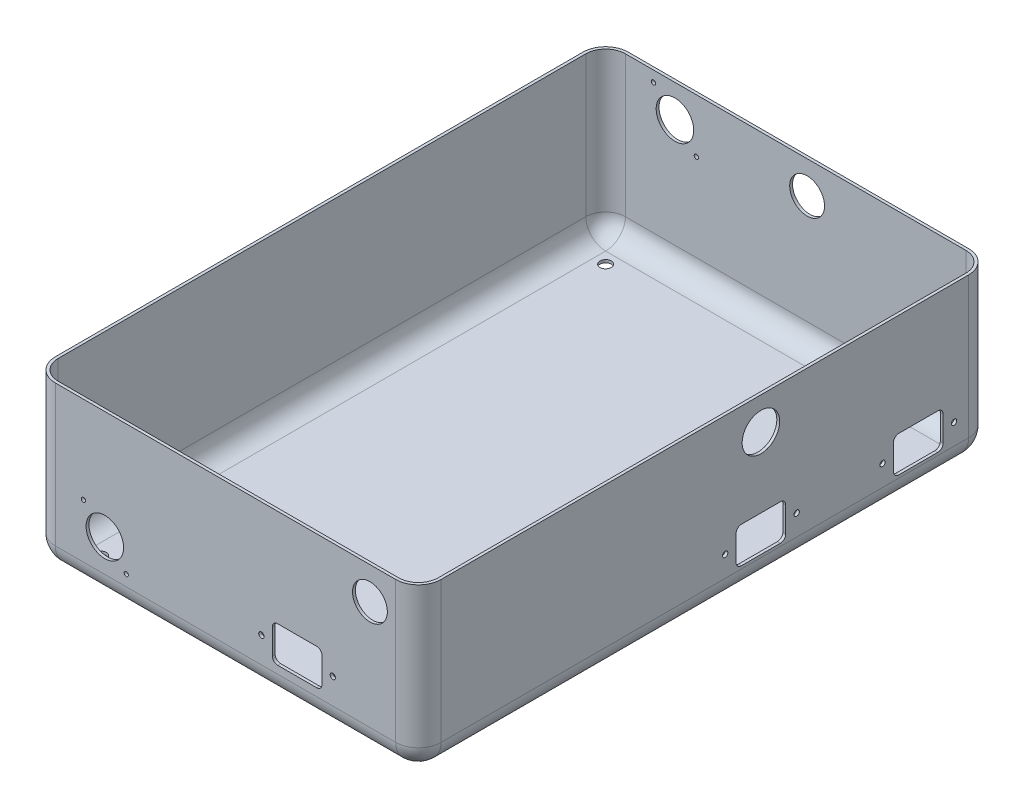
SolidWorks part; units mm, degrees
ref_plane "Front" through (0, 0, 0) normal (0, 0, 1) x (1, 0, 0)
ref_plane "Top" through (0, 0, 0) normal (0, 1, 0) x (1, 0, 0)
ref_plane "Right" through (0, 0, 0) normal (1, 0, 0) x (0, 0, -1)
sketch "Sketch1" plane through (0, 0, 0) normal (0, 1, 0) x (1, 0, 0)
  line L1 (0, 0) -> (215.9, 0)
  line L2 (0, 0) -> (0, 320.675)
  line L3 (0, 320.675) -> (215.9, 320.675)
  line L4 (215.9, 0) -> (215.9, 320.675)
  dimension "D1" = 215.9
  dimension "D2" = 320.675
extrude "Boss-Extrude1" add sketch "Sketch1" along normal blind 91.6889 contours L1 L4 L3 L2
fillet "Fillet1" radius 12.7 8 edges at (0, 45.8445, -320.675) (215.9, 45.8445, -320.675) (215.9, 45.8445, 0) (0, 45.8445, 0) (107.95, 0, -320.675) (0, 0, -160.3375) (107.95, 0, 0) (215.9, 0, -160.3375)
shell "Shell1" thickness 1.6002
sketch "Sketch2" plane through (215.9, 0, 0) normal (1, 0, 0) x (0, 0, -1)
  line L0 (168.1645, 20.8147) -> (175.0003, 13.9789) construction
  line L1 (177.1216, 13.1002) -> (206.2784, 13.1002) construction
  line L2 (208.3997, 13.9789) -> (215.2355, 20.8147) construction
  line L3 (215.2355, 27.8857) -> (208.3997, 34.7215) construction
  line L4 (206.2784, 35.6002) -> (177.1216, 35.6002) construction
  line L5 (175.0003, 34.7215) -> (168.1645, 27.8857) construction
  line L7 (307.975, 12.7) -> (307.975, 91.6889) construction
  line L9 (12.7, 91.6889) -> (12.7, 12.7) construction
  line L10 (168.1645, 20.8147) -> (175.0003, 13.9789)
  line L11 (177.1216, 13.1002) -> (206.2784, 13.1002)
  line L12 (208.3997, 13.9789) -> (215.2355, 20.8147)
  line L13 (215.2355, 27.8857) -> (208.3997, 34.7215)
  line L14 (206.2784, 35.6002) -> (177.1216, 35.6002)
  line L15 (175.0003, 34.7215) -> (168.1645, 27.8857)
  line L16 (12.7, 12.7) -> (307.975, 12.7)
  line L17 (307.975, 12.7) -> (307.975, 91.6889)
  line L18 (307.975, 91.6889) -> (12.7, 91.6889)
  line L19 (12.7, 91.6889) -> (12.7, 12.7)
  line L20 (205.6, 31.4002) -> (205.6, 17.3002) construction
  line L21 (202.6, 14.3002) -> (180.8, 14.3002) construction
  line L22 (177.8, 17.3002) -> (177.8, 31.4002) construction
  line L23 (180.8, 34.4002) -> (202.6, 34.4002) construction
  line L24 (293.7, 31.4002) -> (293.7, 17.3002) construction
  line L25 (290.7, 14.3002) -> (268.9, 14.3002) construction
  line L26 (256.2645, 20.8147) -> (263.1003, 13.9789)
  line L27 (265.2216, 13.1002) -> (294.3784, 13.1002)
  line L28 (296.4997, 13.9789) -> (303.3355, 20.8147)
  line L29 (303.3355, 27.8857) -> (296.4997, 34.7215)
  line L30 (294.3784, 35.6002) -> (265.2216, 35.6002)
  line L31 (263.1003, 34.7215) -> (256.2645, 27.8857)
  line L32 (256.2645, 20.8147) -> (263.1003, 13.9789)
  line L33 (265.2216, 13.1002) -> (294.3784, 13.1002)
  line L34 (296.4997, 13.9789) -> (303.3355, 20.8147)
  line L35 (303.3355, 27.8857) -> (296.4997, 34.7215)
  line L36 (294.3784, 35.6002) -> (265.2216, 35.6002)
  line L37 (263.1003, 34.7215) -> (256.2645, 27.8857)
  line L38 (265.9, 17.3002) -> (265.9, 31.4002) construction
  line L39 (268.9, 34.4002) -> (290.7, 34.4002) construction
  line L40 (205.6, 31.4002) -> (205.6, 17.3002)
  line L41 (202.6, 14.3002) -> (180.8, 14.3002)
  line L42 (177.8, 17.3002) -> (177.8, 31.4002)
  line L43 (180.8, 34.4002) -> (202.6, 34.4002)
  line L44 (293.7, 31.4002) -> (293.7, 17.3002)
  line L45 (290.7, 14.3002) -> (268.9, 14.3002)
  line L46 (265.9, 17.3002) -> (265.9, 31.4002)
  line L47 (268.9, 34.4002) -> (290.7, 34.4002)
  line L48 (12.7, 12.7) -> (307.975, 12.7) construction
  line L49 (12.7, 91.6889) -> (307.975, 91.6889) construction
  arc A0 (168.1645, 27.8857) -> (168.1645, 20.8147) centre (171.7, 24.3502) ccw construction
  arc A1 (175.0003, 13.9789) -> (177.1216, 13.1002) centre (177.1216, 16.1002) ccw construction
  arc A2 (206.2784, 13.1002) -> (208.3997, 13.9789) centre (206.2784, 16.1002) ccw construction
  arc A3 (215.2355, 20.8147) -> (215.2355, 27.8857) centre (211.7, 24.3502) ccw construction
  arc A4 (208.3997, 34.7215) -> (206.2784, 35.6002) centre (206.2784, 32.6002) ccw construction
  arc A5 (177.1216, 35.6002) -> (175.0003, 34.7215) centre (177.1216, 32.6002) ccw construction
  arc A6 (168.1645, 27.8857) -> (168.1645, 20.8147) centre (171.7, 24.3502) ccw
  arc A7 (175.0003, 13.9789) -> (177.1216, 13.1002) centre (177.1216, 16.1002) ccw
  arc A8 (206.2784, 13.1002) -> (208.3997, 13.9789) centre (206.2784, 16.1002) ccw
  arc A9 (215.2355, 20.8147) -> (215.2355, 27.8857) centre (211.7, 24.3502) ccw
  arc A10 (208.3997, 34.7215) -> (206.2784, 35.6002) centre (206.2784, 32.6002) ccw
  arc A11 (177.1216, 35.6002) -> (175.0003, 34.7215) centre (177.1216, 32.6002) ccw
  circle A12 centre (171.7, 24.3502) radius 1.5 construction
  circle A13 centre (211.7, 24.3502) radius 1.5 construction
  circle A14 centre (171.7, 24.3502) radius 1.5
  circle A15 centre (211.7, 24.3502) radius 1.5
  arc A16 (200.8, 78.8704) -> (200.1022, 67.3349) centre (191.7, 73.6321) ccw construction
  arc A17 (200.8, 78.8704) -> (202.2, 73.6321) centre (191.7, 73.6321) ccw
  arc A19 (200.8, 78.8704) -> (202.2, 73.6321) centre (191.7, 73.6321) cw
  circle A20 centre (299.8, 24.3502) radius 1.5 construction
  circle A21 centre (259.8, 24.3502) radius 1.5 construction
  circle A22 centre (299.8, 24.3502) radius 1.5
  circle A23 centre (259.8, 24.3502) radius 1.5
  arc A24 (205.6, 31.4002) -> (202.6, 34.4002) centre (202.6, 31.4002) ccw construction
  arc A25 (202.6, 14.3002) -> (205.6, 17.3002) centre (202.6, 17.3002) ccw construction
  arc A26 (177.8, 17.3002) -> (180.8, 14.3002) centre (180.8, 17.3002) ccw construction
  arc A27 (180.8, 34.4002) -> (177.8, 31.4002) centre (180.8, 31.4002) ccw construction
  arc A28 (293.7, 31.4002) -> (290.7, 34.4002) centre (290.7, 31.4002) ccw construction
  arc A29 (290.7, 14.3002) -> (293.7, 17.3002) centre (290.7, 17.3002) ccw construction
  arc A30 (256.2645, 27.8857) -> (256.2645, 20.8147) centre (259.8, 24.3502) ccw
  arc A31 (263.1003, 13.9789) -> (265.2216, 13.1002) centre (265.2216, 16.1002) ccw
  arc A32 (294.3784, 13.1002) -> (296.4997, 13.9789) centre (294.3784, 16.1002) ccw
  arc A33 (303.3355, 20.8147) -> (303.3355, 27.8857) centre (299.8, 24.3502) ccw
  arc A34 (296.4997, 34.7215) -> (294.3784, 35.6002) centre (294.3784, 32.6002) ccw
  arc A35 (265.2216, 35.6002) -> (263.1003, 34.7215) centre (265.2216, 32.6002) ccw
  arc A36 (256.2645, 27.8857) -> (256.2645, 20.8147) centre (259.8, 24.3502) ccw
  arc A37 (263.1003, 13.9789) -> (265.2216, 13.1002) centre (265.2216, 16.1002) ccw
  arc A38 (294.3784, 13.1002) -> (296.4997, 13.9789) centre (294.3784, 16.1002) ccw
  arc A39 (303.3355, 20.8147) -> (303.3355, 27.8857) centre (299.8, 24.3502) ccw
  arc A40 (296.4997, 34.7215) -> (294.3784, 35.6002) centre (294.3784, 32.6002) ccw
  arc A41 (265.2216, 35.6002) -> (263.1003, 34.7215) centre (265.2216, 32.6002) ccw
  arc A42 (265.9, 17.3002) -> (268.9, 14.3002) centre (268.9, 17.3002) ccw construction
  arc A43 (268.9, 34.4002) -> (265.9, 31.4002) centre (268.9, 31.4002) ccw construction
  arc A44 (205.6, 31.4002) -> (202.6, 34.4002) centre (202.6, 31.4002) ccw
  arc A45 (202.6, 14.3002) -> (205.6, 17.3002) centre (202.6, 17.3002) ccw
  arc A46 (177.8, 17.3002) -> (180.8, 14.3002) centre (180.8, 17.3002) ccw
  arc A47 (180.8, 34.4002) -> (177.8, 31.4002) centre (180.8, 31.4002) ccw
  arc A48 (293.7, 31.4002) -> (290.7, 34.4002) centre (290.7, 31.4002) ccw
  arc A49 (290.7, 14.3002) -> (293.7, 17.3002) centre (290.7, 17.3002) ccw
  arc A50 (265.9, 17.3002) -> (268.9, 14.3002) centre (268.9, 17.3002) ccw
  arc A51 (268.9, 34.4002) -> (265.9, 31.4002) centre (268.9, 31.4002) ccw
  dimension "D1" = 0
extrude "Cut-Extrude1" cut sketch "Sketch2" against normal up to next contours A19 A17 | A14 | A15 | A23 | A22 | L47 A51 L46 A50 L45 A49 L44 A48 | L43 A47 L42 A46 L41 A45 L40 A44
sketch "Sketch5" plane through (317.5, 0, 0) normal (0, 0, 1) x (1, 0, 0)
  line L0 (-180.375, 37.175) -> (-158.575, 37.175) construction
  line L1 (-183.375, 20.075) -> (-183.375, 34.175) construction
  line L2 (-158.575, 17.075) -> (-180.375, 17.075) construction
  line L3 (-155.575, 34.175) -> (-155.575, 20.075) construction
  line L4 (-180.375, 37.175) -> (-158.575, 37.175)
  line L5 (-183.375, 20.075) -> (-183.375, 34.175)
  line L6 (-158.575, 17.075) -> (-180.375, 17.075)
  line L7 (-155.575, 34.175) -> (-155.575, 20.075)
  arc A2 (-123.85, 65.1883) -> (-133.6, 82.0758) centre (-128.725, 73.6321) ccw construction
  arc A3 (-133.6, 82.0758) -> (-123.85, 65.1883) centre (-128.725, 73.6321) ccw construction
  arc A6 (-123.85, 65.1883) -> (-133.6, 82.0758) centre (-128.725, 73.6321) ccw
  arc A7 (-133.6, 82.0758) -> (-123.85, 65.1883) centre (-128.725, 73.6321) ccw
  circle A8 centre (-189.475, 27.125) radius 1.5 construction
  circle A9 centre (-149.475, 27.125) radius 1.5 construction
  arc A10 (-155.575, 34.175) -> (-158.575, 37.175) centre (-158.575, 34.175) ccw construction
  arc A11 (-180.375, 37.175) -> (-183.375, 34.175) centre (-180.375, 34.175) ccw construction
  arc A12 (-183.375, 20.075) -> (-180.375, 17.075) centre (-180.375, 20.075) ccw construction
  arc A13 (-158.575, 17.075) -> (-155.575, 20.075) centre (-158.575, 20.075) ccw construction
  circle A14 centre (-189.475, 27.125) radius 1.5
  circle A15 centre (-149.475, 27.125) radius 1.5
  arc A16 (-155.575, 34.175) -> (-158.575, 37.175) centre (-158.575, 34.175) ccw
  arc A17 (-180.375, 37.175) -> (-183.375, 34.175) centre (-180.375, 34.175) ccw
  arc A18 (-183.375, 20.075) -> (-180.375, 17.075) centre (-180.375, 20.075) ccw
  arc A19 (-158.575, 17.075) -> (-155.575, 20.075) centre (-158.575, 20.075) ccw
  circle A20 centre (-289.1, 42.875) radius 1.2 construction
  circle A21 centre (-265.1, 18.875) radius 1.2 construction
  circle A22 centre (-277.1, 30.875) radius 10.5 construction
  circle A23 centre (-289.1, 42.875) radius 1.2
  circle A24 centre (-265.1, 18.875) radius 1.2
  circle A25 centre (-277.1, 30.875) radius 10.5
extrude "Cut-Extrude2" cut sketch "Sketch5" against normal up to next
sketch "Sketch6" plane through (0, 0, -320.675) normal (0, 0, -1) x (-1, 0, 0)
  arc A0 (-109.5052, 65.1883) -> (-119.2552, 82.0758) centre (-114.3802, 73.6321) ccw construction
  arc A1 (-119.2552, 82.0758) -> (-109.5052, 65.1883) centre (-114.3802, 73.6321) ccw construction
  arc A2 (-109.5052, 65.1883) -> (-119.2552, 82.0758) centre (-114.3802, 73.6321) ccw
  arc A3 (-119.2552, 82.0758) -> (-109.5052, 65.1883) centre (-114.3802, 73.6321) ccw
  circle A4 centre (-28.4, 85.6321) radius 1.2 construction
  circle A5 centre (-52.4, 61.6321) radius 1.2 construction
  circle A6 centre (-40.4, 73.6321) radius 10.5 construction
  circle A7 centre (-28.4, 85.6321) radius 1.2
  circle A8 centre (-52.4, 61.6321) radius 1.2
  circle A9 centre (-40.4, 73.6321) radius 10.5
extrude "Cut-Extrude3" cut sketch "Sketch6" against normal up to next
sketch "Sketch7" plane through (0, 0, 0) normal (0, -1, 0) x (1, 0, 0)
  line L0 (203.2, -12.7) -> (12.7, -12.7) construction
  line L1 (203.2, -307.975) -> (203.2, -12.7) construction
  line L2 (12.7, -307.975) -> (203.2, -307.975) construction
  line L3 (12.7, -12.7) -> (12.7, -307.975) construction
  line L4 (203.2, -12.7) -> (12.7, -12.7) construction
  line L5 (203.2, -307.975) -> (203.2, -12.7) construction
  line L6 (12.7, -307.975) -> (203.2, -307.975) construction
  line L7 (12.7, -12.7) -> (12.7, -307.975) construction
  line L8 (19.05, -301.625) -> (196.85, -301.625) construction
  line L9 (196.85, -301.625) -> (196.85, -19.05) construction
  line L10 (196.85, -19.05) -> (19.05, -19.05) construction
  line L11 (19.05, -19.05) -> (19.05, -301.625) construction
  line L12 (190.5, -298.4455) -> (190.5, -283.4471) construction
  line L15 (192.0536, -301.625) -> (188.9464, -301.625) construction
  line L16 (188.9464, 9.6951) -> (188.9464, -330.3701) construction
  line L17 (192.0536, 9.6951) -> (192.0536, -330.3701) construction
  circle A1 centre (19.05, -301.625) radius 3.175
  circle A4 centre (19.05, -19.05) radius 3.175
  circle A5 centre (139.7, -100.34) radius 3.175
  circle A6 centre (165.1, -100.34) radius 3.175
  circle A7 centre (139.7, -220.335) radius 3.175
  circle A9 centre (168.275, -301.625) radius 3.175
  circle A10 centre (168.275, -19.05) radius 3.175
  circle A12 centre (139.7, -100.34) radius 3.2639 construction
  circle A15 centre (165.1, -100.34) radius 3.2639 construction
  circle A17 centre (139.7, -220.335) radius 3.2639 construction
  circle A19 centre (165.1, -220.335) radius 3.175
  circle A20 centre (165.1, -220.335) radius 3.2639 construction
  point P23 (190.5, -301.625)
  point P31 (171.45, -301.625)
  dimension "D2" = 6.35
  dimension "D3" = 6.35
  dimension "D6" = 25.4
  dimension "D1" = 6.35
extrude "Cut-Extrude4" cut sketch "Sketch7" against normal up to next
